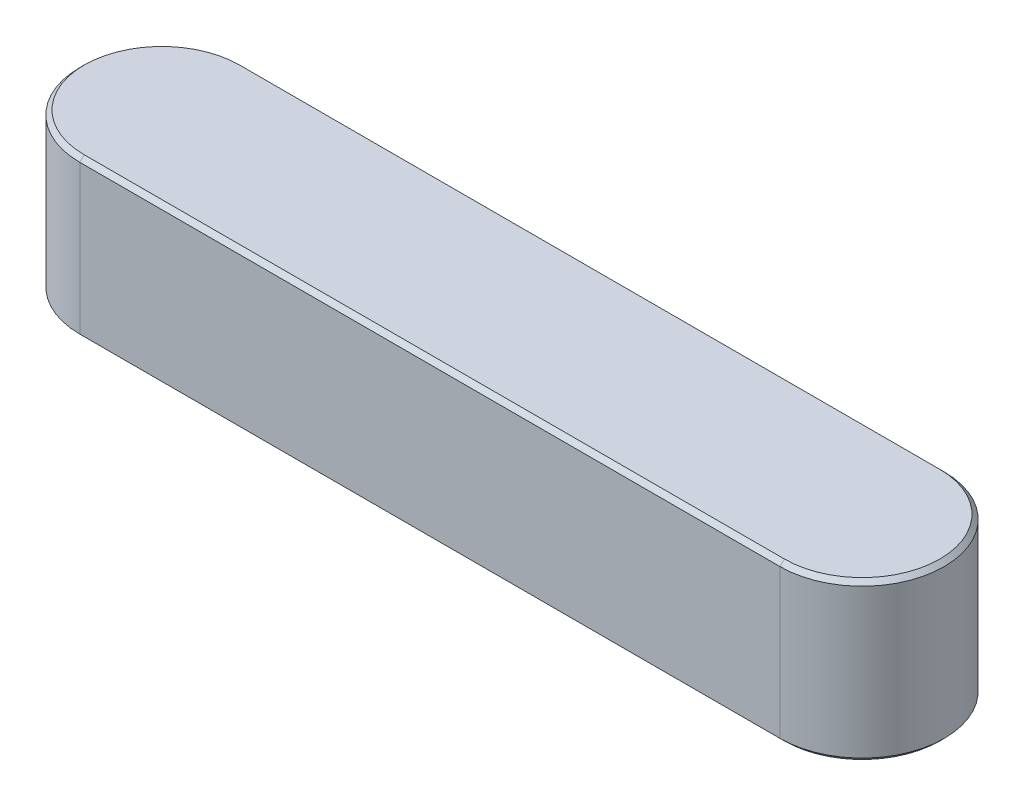
SolidWorks part; units mm, degrees
ref_plane "Front Plane" through (0, 0, 0) normal (0, 0, 1) x (1, 0, 0)
ref_plane "Top Plane" through (0, 0, 0) normal (0, 1, 0) x (1, 0, 0)
ref_plane "Right Plane" through (0, 0, 0) normal (1, 0, 0) x (0, 0, -1)
sketch "Sketch1" plane through (0, 0, 0) normal (0, 1, 0) x (1, 0, 0)
  line L0 (0.4, 0) -> (-0.4, 0) construction
  line L1 (0.4, -0.0937) -> (-0.4, -0.0938)
  line L2 (0.4, 0.0938) -> (-0.4, 0.0937)
  arc A0 (0.4, -0.0937) -> (0.4, 0.0938) centre (0.4, 0) ccw
  arc A1 (-0.4, 0.0937) -> (-0.4, -0.0938) centre (-0.4, 0) ccw
  point P2 (0, 0)
  dimension "D2" = 0.0938
  dimension "D1" = 0.1875
  dimension "D3" = 0.8
extrude "Boss-Extrude1" add sketch "Sketch1" along normal mid plane 0.18
chamfer "Chamfer1" distance 0.005 angle 45 8 edges at (0, -0.09, -0.0938) (-0.4937, -0.09, 0) (0, -0.09, 0.0937) (0.4937, -0.09, 0) (0, 0.09, 0.0937) (-0.4937, 0.09, 0) (0, 0.09, -0.0938) (0.4937, 0.09, 0)
